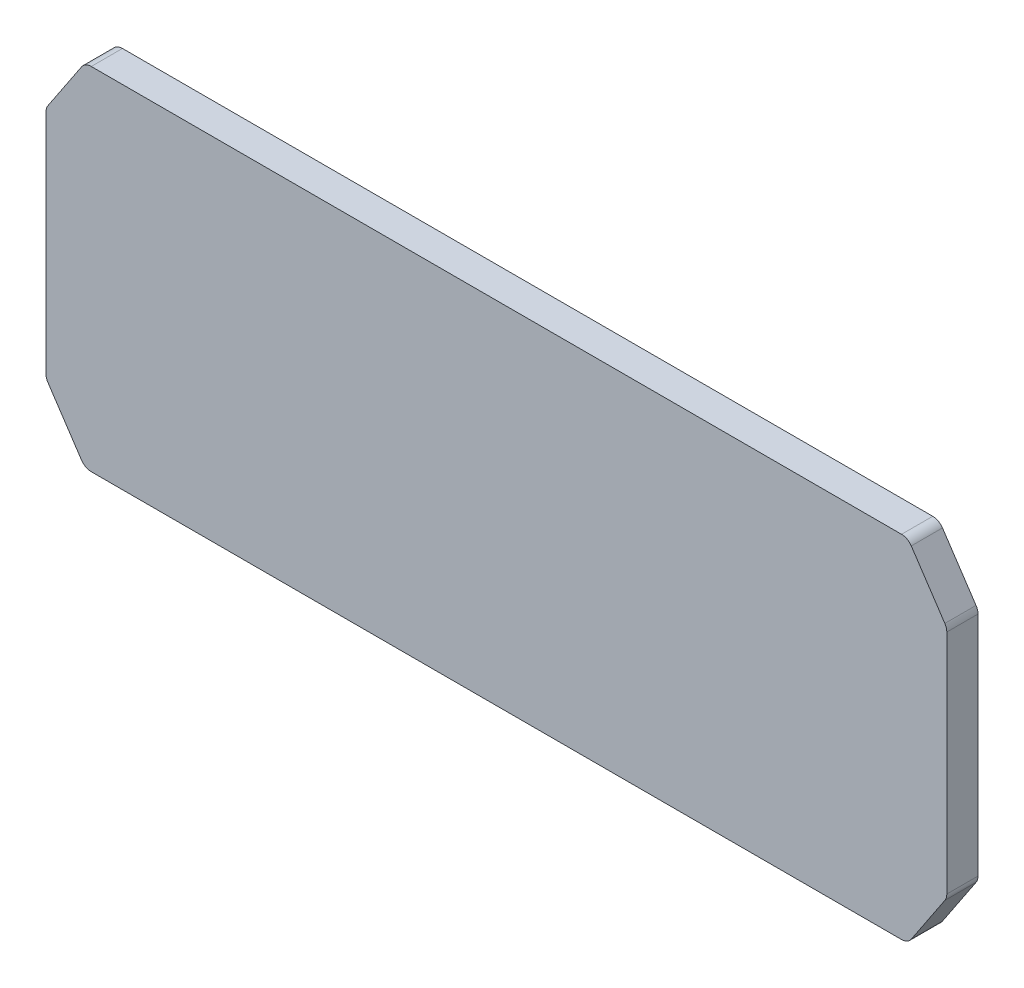
SolidWorks part; units mm, degrees
ref_plane "Plane1" through (0, 0, 0) normal (0, 0, 1) x (1, 0, 0)
ref_plane "Plane2" through (0, 0, 0) normal (0, 1, 0) x (1, 0, 0)
ref_plane "Plane3" through (0, 0, 0) normal (1, 0, 0) x (0, 0, -1)
sketch "Sketch1" plane through (0, 0, 0) normal (0, 0, 1) x (1, 0, 0)
  line L0 (106.3906, 1.3359) -> (114.9962, 14.2442)
  line L1 (-103.8944, 0) -> (103.8944, 0)
  line L2 (-115.5, 15.9083) -> (-115.5, 74.0917)
  line L3 (-103.8944, 90) -> (103.8944, 90)
  line L4 (115.5, 15.9083) -> (115.5, 74.0917)
  line L5 (114.9962, 75.7558) -> (106.3906, 88.6641)
  line L6 (0, 0) -> (0, 58) construction
  line L7 (-106.3906, 1.3359) -> (-114.9962, 14.2442)
  line L8 (-114.9962, 75.7558) -> (-106.3906, 88.6641)
  arc A0 (106.3906, 1.3359) -> (103.8944, 0) centre (103.8944, 3) cw
  arc A1 (-106.3906, 1.3359) -> (-103.8944, 0) centre (-103.8944, 3) ccw
  arc A2 (-114.9962, 14.2442) -> (-115.5, 15.9083) centre (-112.5, 15.9083) cw
  arc A3 (114.9962, 14.2442) -> (115.5, 15.9083) centre (112.5, 15.9083) ccw
  arc A4 (114.9962, 75.7558) -> (115.5, 74.0917) centre (112.5, 74.0917) cw
  arc A5 (106.3906, 88.6641) -> (103.8944, 90) centre (103.8944, 87) ccw
  arc A6 (-106.3906, 88.6641) -> (-103.8944, 90) centre (-103.8944, 87) cw
  arc A7 (-114.9962, 75.7558) -> (-115.5, 74.0917) centre (-112.5, 74.0917) ccw
  point P2 (105.5, 0)
  point P15 (-105.5, 0)
  point P18 (-115.5, 15)
  point P21 (115.5, 15)
  point P24 (115.5, 75)
  point P27 (105.5, 90)
  point P30 (-105.5, 90)
  point P33 (-115.5, 75)
  dimension "D7" = 3
  dimension "D1" = 231
  dimension "D2" = 90
  dimension "D3" = 10
  dimension "D4" = 15
  dimension "D5" = 15
  dimension "D6" = 10
extrude "Extrude1" add sketch "Sketch1" along normal blind 8
chamfer "Chamfer1" [suppressed] distance 6 angle 45
